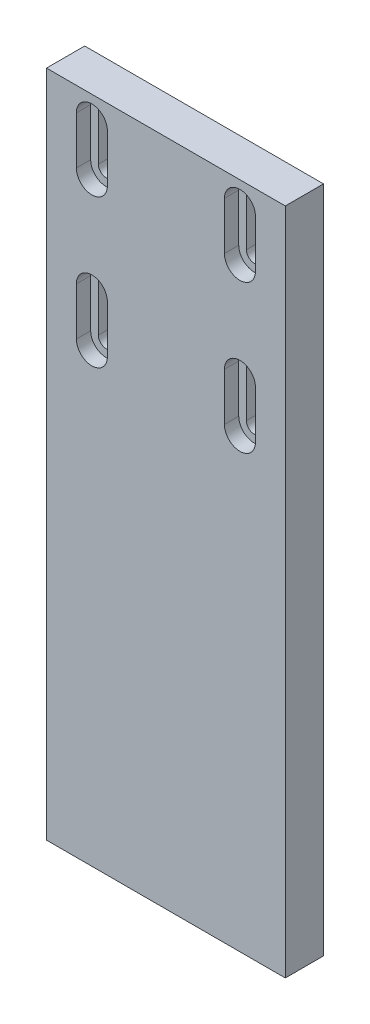
SolidWorks part; units mm, degrees
ref_plane "前基準面" through (0, 0, 0) normal (0, 0, 1) x (1, 0, 0)
ref_plane "上基準面" through (0, 0, 0) normal (0, 1, 0) x (1, 0, 0)
ref_plane "右基準面" through (0, 0, 0) normal (1, 0, 0) x (0, 0, -1)
sketch "草圖1" plane through (0, 0, 0) normal (0, 0, 1) x (1, 0, 0)
  line L1 (-25, -70) -> (25, -70)
  line L2 (-25, -70) -> (-25, 70)
  line L3 (-25, 70) -> (25, 70)
  line L4 (25, -70) -> (25, 70)
  line L5 (-25, -70) -> (25, 70) construction
  line L6 (-25, 70) -> (25, -70) construction
  point P0 (0, 0)
  dimension "D1" = 50
  dimension "D2" = 140
extrude "填料-伸長1" add sketch "草圖1" along normal blind 8
sketch "草圖8" plane through (0, 0, 8) normal (0, 0, 1) x (1, 0, 0)
  line L0 (25, 70) -> (-25, 70) construction
  line L1 (-15.5, 60) -> (15.5, 60) construction
  line L2 (-15.5, 60) -> (-15.5, 29) construction
  line L3 (-15.5, 29) -> (15.5, 29) construction
  line L4 (15.5, 60) -> (15.5, 29) construction
  line L5 (-15.5, 65) -> (-15.5, 55) construction
  line L6 (-13.85, 65) -> (-13.85, 55)
  line L7 (-17.15, 65) -> (-17.15, 55)
  line L8 (13.85, 65) -> (13.85, 55)
  line L9 (17.15, 65) -> (17.15, 55)
  line L10 (15.5, 65) -> (15.5, 55) construction
  line L11 (13.85, 34) -> (13.85, 24)
  line L12 (17.15, 34) -> (17.15, 24)
  line L13 (15.5, 34) -> (15.5, 24) construction
  line L14 (-17.15, 34) -> (-17.15, 24)
  line L15 (-13.85, 34) -> (-13.85, 24)
  line L16 (-15.5, 34) -> (-15.5, 24) construction
  arc A0 (-13.85, 65) -> (-17.15, 65) centre (-15.5, 65) ccw
  arc A1 (-17.15, 55) -> (-13.85, 55) centre (-15.5, 55) ccw
  arc A2 (17.15, 65) -> (13.85, 65) centre (15.5, 65) ccw
  arc A3 (13.85, 55) -> (17.15, 55) centre (15.5, 55) ccw
  arc A4 (17.15, 34) -> (13.85, 34) centre (15.5, 34) ccw
  arc A5 (13.85, 24) -> (17.15, 24) centre (15.5, 24) ccw
  arc A6 (-13.85, 34) -> (-17.15, 34) centre (-15.5, 34) ccw
  arc A7 (-17.15, 24) -> (-13.85, 24) centre (-15.5, 24) ccw
  point P6 (0, 60)
  point P7 (0, 70)
  point P10 (-15.5, 60)
  point P16 (0, 0)
  point P17 (0, 0)
  point P19 (15.5, 60)
  point P26 (15.5, 29)
  point P33 (-15.5, 29)
  dimension "D1" = 10
  dimension "D2" = 31
  dimension "D3" = 10
  dimension "D4" = 3.3
  dimension "D5" = 2
  dimension "D6" = 2
extrude "除料-伸長2" cut sketch "草圖8" against normal blind 8
sketch "草圖9" plane through (0, 0, 8) normal (0, 0, 1) x (1, 0, 0)
  line L0 (-15.5, 65) -> (-15.5, 55) construction
  line L1 (-12.25, 65) -> (-12.25, 55)
  line L2 (-18.75, 65) -> (-18.75, 55)
  line L3 (12.25, 65) -> (12.25, 55)
  line L4 (18.75, 65) -> (18.75, 55)
  line L5 (15.5, 65) -> (15.5, 55) construction
  line L6 (12.25, 34) -> (12.25, 24)
  line L7 (18.75, 34) -> (18.75, 24)
  line L8 (15.5, 34) -> (15.5, 24) construction
  line L9 (-18.75, 34) -> (-18.75, 24)
  line L10 (-12.25, 34) -> (-12.25, 24)
  line L11 (-15.5, 34) -> (-15.5, 24) construction
  line L12 (-25, 70) -> (-25, -70) construction
  arc A0 (-12.25, 65) -> (-18.75, 65) centre (-15.5, 65) ccw
  arc A1 (-18.75, 55) -> (-12.25, 55) centre (-15.5, 55) ccw
  arc A2 (18.75, 65) -> (12.25, 65) centre (15.5, 65) ccw
  arc A3 (12.25, 55) -> (18.75, 55) centre (15.5, 55) ccw
  arc A4 (18.75, 34) -> (12.25, 34) centre (15.5, 34) ccw
  arc A5 (12.25, 24) -> (18.75, 24) centre (15.5, 24) ccw
  arc A6 (-12.25, 34) -> (-18.75, 34) centre (-15.5, 34) ccw
  arc A7 (-18.75, 24) -> (-12.25, 24) centre (-15.5, 24) ccw
  point P2 (-15.5, 60)
  point P10 (0, 0)
  point P11 (0, 0)
  point P13 (15.5, 60)
  point P20 (15.5, 29)
  point P27 (-15.5, 29)
  dimension "D1" = 6.5
  dimension "D4" = 31
  dimension "D5" = 6.25
  dimension "D2" = 2
  dimension "D3" = 2
extrude "除料-伸長3" cut sketch "草圖9" against normal blind 3
